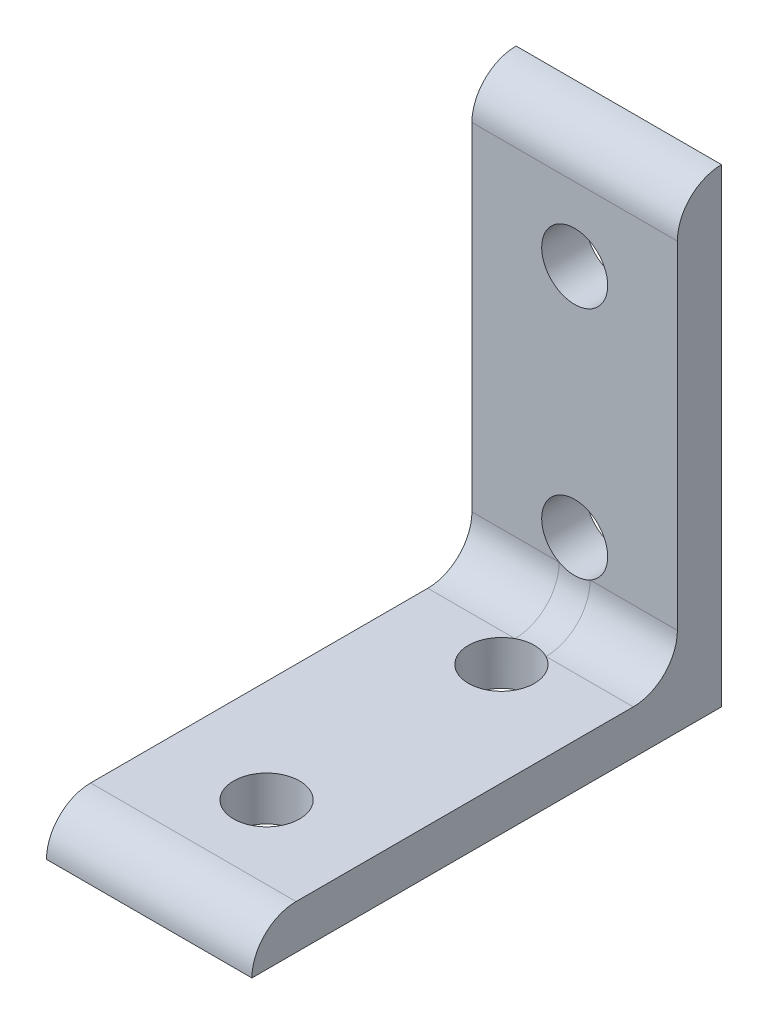
SolidWorks part; units mm, degrees
material "6061 Alloy"
ref_plane "Front Plane" through (0, 0, 0) normal (0, 0, 1) x (1, 0, 0)
ref_plane "Top Plane" through (0, 0, 0) normal (0, 1, 0) x (1, 0, 0)
ref_plane "Right Plane" through (0, 0, 0) normal (1, 0, 0) x (0, 0, -1)
sketch "Sketch1" plane through (0, 0, 0) normal (1, 0, 0) x (0, 0, -1)
  line L0 (-28.1992, 21.8977) -> (22.6008, 21.8977)
  line L1 (22.6008, 21.8977) -> (17.8256, 26.6729)
  line L2 (-23.424, 26.6729) -> (17.8256, 26.6729)
  line L3 (-28.1992, 26.6729) -> (22.6008, 26.6729) construction
  arc A0 (-23.424, 26.6729) -> (-28.1992, 21.8977) centre (-23.424, 21.8977) ccw
  dimension "D1" = 4.7752
extrude "Extrude1" add sketch "Sketch1" along normal blind 22.225
sketch "Sketch2" plane through (0, 26.6729, 0) normal (0, 1, 0) x (1, 0, 0)
  circle A0 centre (11.1125, -15.4992) radius 3.5687
  circle A1 centre (11.1125, 9.9008) radius 3.5687
extrude "Cut-Extrude1" cut sketch "Sketch2" against normal through all
mirror "Mirror1" about plane through (22.225, 21.8977, -22.6008) normal (0, -0.7071, 0.7071) of bodies 102
fillet "Fillet1" radius 4.7752 1 edges at (11.1125, 26.6729, -17.8256)
